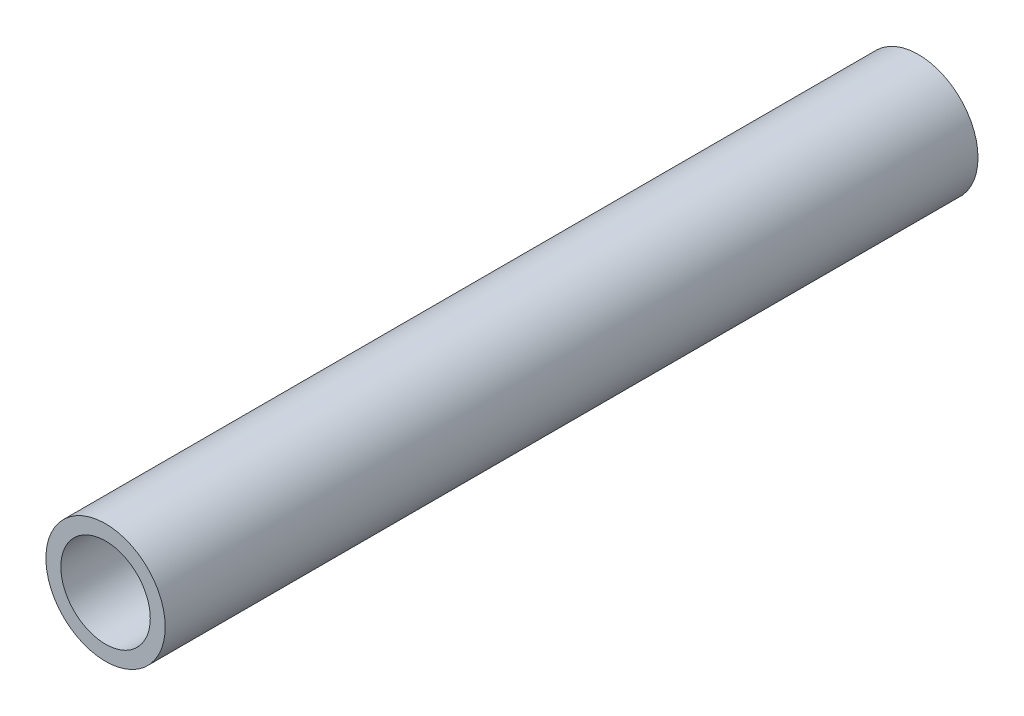
SolidWorks part; units mm, degrees
ref_plane "Front Plane" through (0, 0, 0) normal (0, 0, 1) x (1, 0, 0)
ref_plane "Top Plane" through (0, 0, 0) normal (0, 1, 0) x (1, 0, 0)
ref_plane "Right Plane" through (0, 0, 0) normal (1, 0, 0) x (0, 0, -1)
sketch "Sketch1" plane through (0, 0, 0) normal (0, 0, 1) x (1, 0, 0)
  circle A0 centre (0, 0) radius 4
extrude "Boss-Extrude1" add sketch "Sketch1" along normal blind 54.5
sketch "Sketch2" plane through (0, 0, 54.5) normal (0, 0, 1) x (1, 0, 0)
  circle A0 centre (0, 0) radius 3
extrude "Cut-Extrude1" cut sketch "Sketch2" against normal blind 20.5
